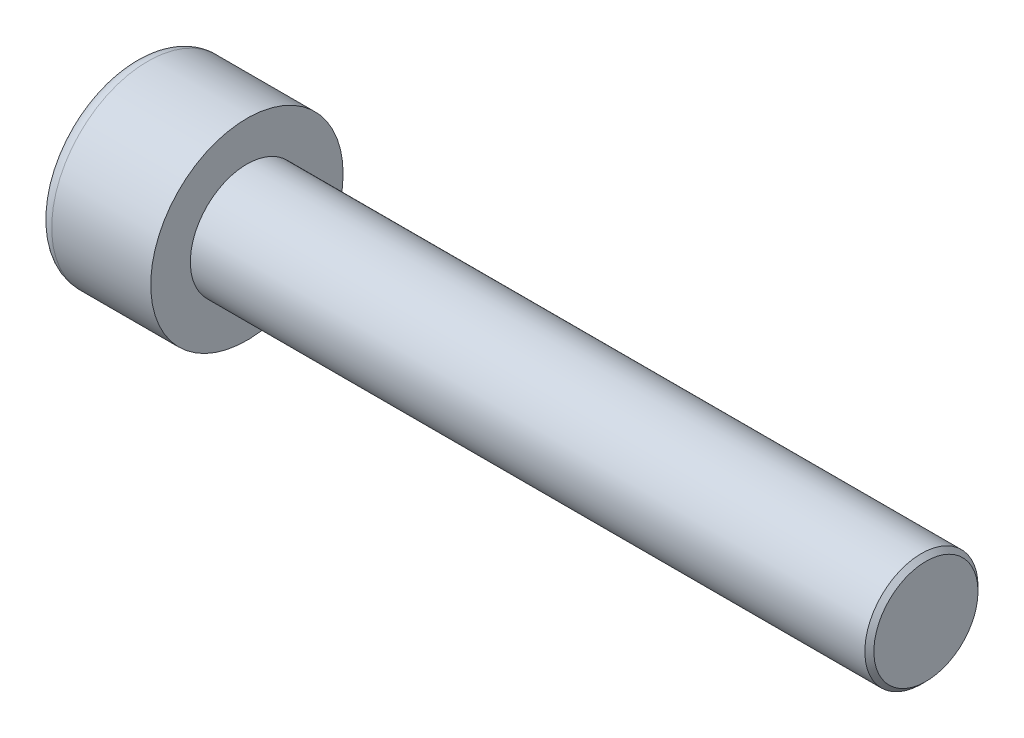
SolidWorks part; units mm, degrees
ref_plane "Front" through (0, 0, 0) normal (0, 0, 1) x (1, 0, 0)
ref_plane "Top" through (0, 0, 0) normal (0, 1, 0) x (1, 0, 0)
ref_plane "Right" through (0, 0, 0) normal (1, 0, 0) x (0, 0, -1)
sketch "Sketch1" plane through (0, 0, 0) normal (1, 0, 0) x (0, 0, -1)
  circle A0 centre (0, 0) radius 4.25
  dimension "dk" = 8.5
extrude "BaseHead" add sketch "Sketch1" along normal blind 5
sketch "Sketch2" plane through (5, 0, 0) normal (1, 0, 0) x (0, 0, -1)
  circle A0 centre (0, 0) radius 2.5
  dimension "d" = 5
extrude "BaseBody" add sketch "Sketch2" along normal blind 30
cosmetic thread "ThreadCosmetic1" parameters "b"=22, "D2"=4.134
sketch "Sketch3" plane through (0, 0, 0) normal (1, 0, 0) x (0, 0, -1)
  line L1 (2.3094, 0) -> (1.1547, 2)
  line L2 (1.1547, 2) -> (-1.1547, 2)
  line L3 (-1.1547, 2) -> (-2.3094, 0)
  line L4 (-2.3094, 0) -> (-1.1547, -2)
  line L5 (-1.1547, -2) -> (1.1547, -2)
  line L6 (1.1547, -2) -> (2.3094, 0)
  circle A0 centre (0, 0) radius 2 construction
  dimension "s" = 4
  dimension "e" = 4.6188
extrude "HexagonSocket" cut sketch "Sketch3" along normal blind 2.5
sketch "Sketch4" plane through (-4.1961, 0.75, 0) normal (0, 0, 1) x (-1, 0, 0)
  line L0 (-6.6961, 2.75) -> (-7.8508, 0.75)
  line L2 (-7.8508, 0.75) -> (-6.6961, 0.75)
  line L3 (-6.6961, 0.75) -> (-6.6961, 2.75)
  line L4 (-5.0351, 0.75) -> (0.839, 0.75) construction
  line L5 (-39.1961, 0.75) -> (-9.1961, 0.75) construction
  line L6 (-9.1961, 0.75) -> (-4.1961, 0.75) construction
  dimension "m" = 60
revolve "Cut-Revolve1" cut sketch "Sketch4" angle 360 about L4
fillet "HeadFillet" [suppressed] radius 0.2
fillet "TopFillet" radius 0.625 1 edges at (0, 0, -4.25)
chamfer "Chamfer1" distance 0.2 angle 45 1 edges at (35, 0, -2.5)
sketch "Sketch5" plane through (0, 0, 0) normal (0, 0, 1) x (1, 0, 0)
  line L0 (34.8, 2.125) -> (35.0165, 2.5)
  line L1 (35.0165, 2.5) -> (35.0165, 2.933)
  line L2 (35.0165, 2.933) -> (34.5835, 2.933)
  line L3 (34.5835, 2.933) -> (34.5835, 2.5)
  line L4 (34.5835, 2.5) -> (34.8, 2.125)
  line L5 (0, 0) -> (7.8886, 0) construction
  line L6 (34.8, -2.5) -> (34.8, 2.5) construction
  dimension "D1" = 5
  dimension "D2" = 0.433
revolve "Cut-Revolve10" [suppressed] cut sketch "Sketch5" angle 360 about L5
pattern_linear "LPattern10" [suppressed] count 42 spacing 0.5196 along (1, 0, 0)
equation "\"r1@TopFillet\" = \"d@Sketch2\" / 8"
equation "\"D1@Chamfer1\" = \"r@HeadFillet\""
equation "\"D1@Sketch5\" = \"d@Sketch2\""
equation "\"D2@Sketch5\" =  ( \"d@Sketch2\" - \"D2@ThreadCosmetic1\" )  / 2"
equation "\"D3@LPattern10\" = \"D2@Sketch5\" * 1.2"
equation "\"D1@LPattern10\" = \"b@ThreadCosmetic1\" / \"D3@LPattern10\""
